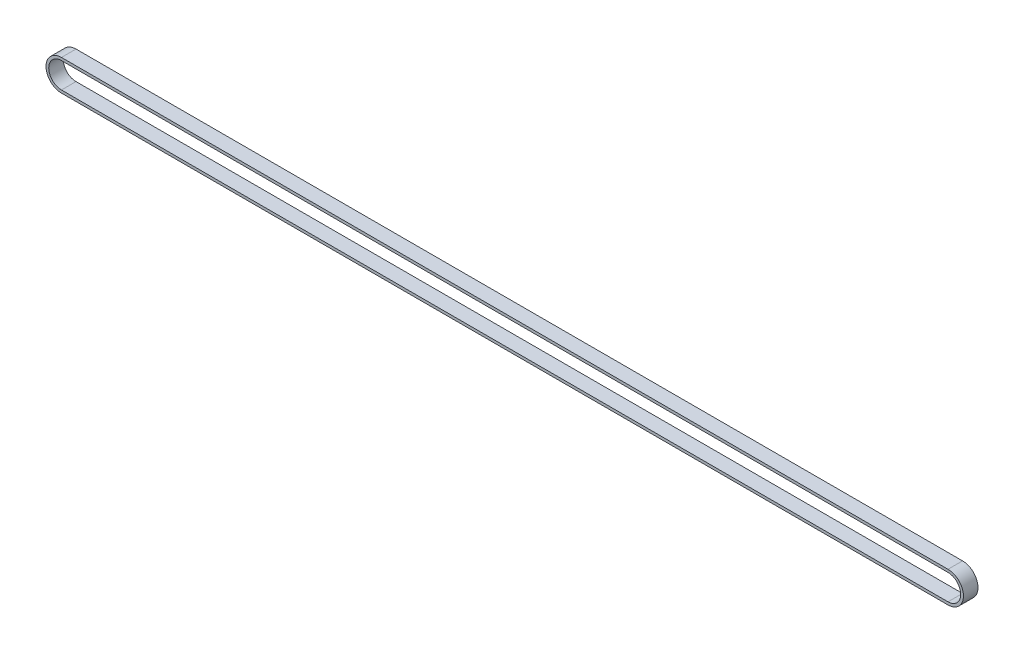
SolidWorks part; units mm, degrees
material "PF"
ref_plane "Piano frontale" through (0, 0, 0) normal (0, 0, 1) x (1, 0, 0)
ref_plane "Piano superiore" through (0, 0, 0) normal (0, 1, 0) x (1, 0, 0)
ref_plane "Piano destro" through (0, 0, 0) normal (1, 0, 0) x (0, 0, -1)
sketch "Schizzo1" plane through (0, 0, 0) normal (0, 0, 1) x (1, 0, 0)
  line L0 (0, 0) -> (-390, 0) construction
  line L1 (0, -5.6) -> (-390, -5.6)
  line L2 (0, 5.6) -> (-390, 5.6)
  line L3 (0, 0) -> (-390, 0) construction
  line L4 (0, -6.8) -> (-390, -6.8)
  line L5 (0, 6.8) -> (-390, 6.8)
  arc A0 (0, -5.6) -> (0, 5.6) centre (0, 0) ccw
  arc A1 (-390, 5.6) -> (-390, -5.6) centre (-390, 0) ccw
  arc A2 (0, -6.8) -> (0, 6.8) centre (0, 0) ccw
  arc A3 (-390, 6.8) -> (-390, -6.8) centre (-390, 0) ccw
  point P3 (-195, 0)
  point P8 (-195, 0)
  dimension "D3" = 5.6
  dimension "D1" = 1.2
  dimension "D2" = 390
extrude "Estrusione-Estrusione1" add sketch "Schizzo1" along normal blind 6.4
